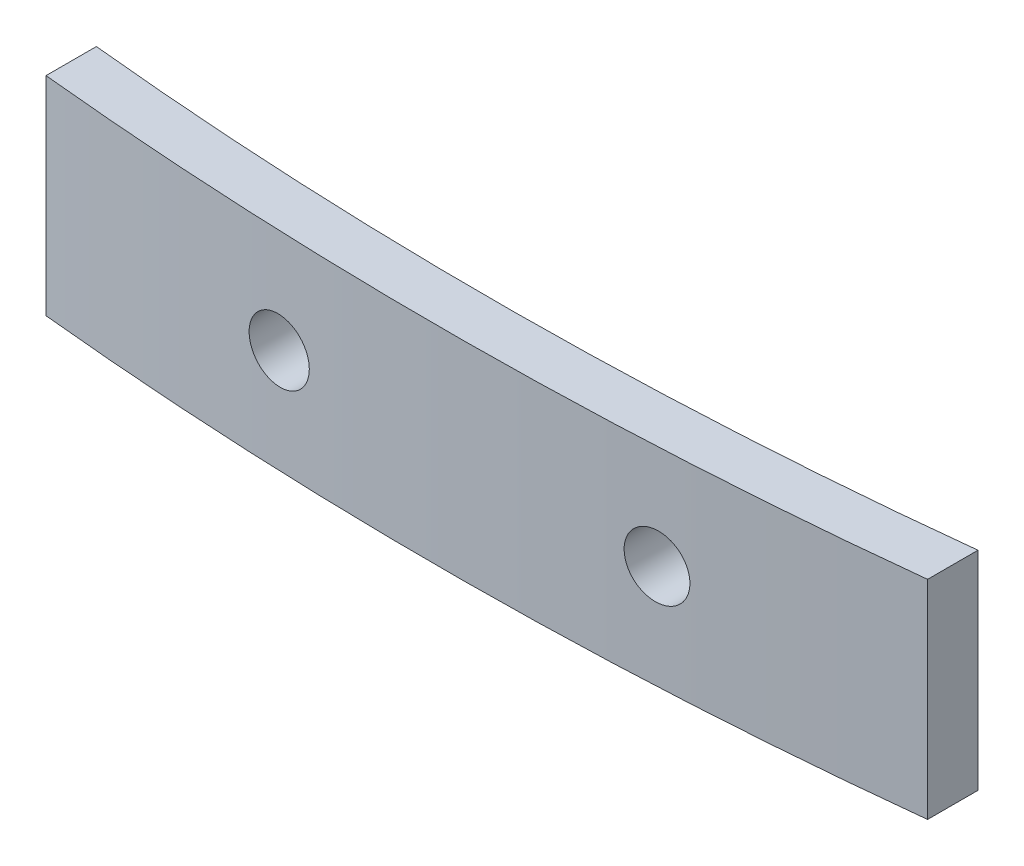
SolidWorks part; units mm, degrees
ref_plane "Front Plane" through (0, 0, 0) normal (0, 0, 1) x (1, 0, 0)
ref_plane "Top Plane" through (0, 0, 0) normal (0, 1, 0) x (1, 0, 0)
ref_plane "Right Plane" through (0, 0, 0) normal (1, 0, 0) x (0, 0, -1)
sketch "Sketch1" plane through (0, 0, 0) normal (0, 1, 0) x (1, 0, 0)
  line L0 (-35, 4.1426) -> (35, 4.5206) construction
  line L3 (-17.5, 11.9983) -> (-17.5, -12.2949) construction
  line L9 (-22.5, 11.9983) -> (-22.5, -12.2817) construction
  line L10 (22.5, 11.9983) -> (22.5, -13.4183) construction
  line L11 (17.5, 11.9983) -> (17.5, -13.4183) construction
  line L13 (-17.5, 0.1395) -> (-17.5, -1.8705)
  line L14 (17.5, 0.3238) -> (17.5, -1.6885)
  arc A4 (-17.5, 0.1395) -> (17.5, 0.3238) centre (-0.865, 164.5106) ccw
  arc A5 (-17.5, -1.8705) -> (17.5, -1.6885) centre (-0.865, 164.5106) ccw
  arc A7 (-35, 2.8648) -> (35, 3.2398) centre (-0.865, 164.5106) ccw construction
  arc A9 (-35.4132, 0.908) -> (35.4342, 1.2875) centre (-0.865, 164.5106) ccw construction
  point P4 (-35, 4.1426)
  point P7 (38.108, 5.4708)
  point P8 (35, 4.5206)
  point P18 (-31.892, 5.0928)
  dimension "D1" = 45
  dimension "D2" = 22.5
  dimension "D3" = 70
  dimension "D4" = 35
  dimension "D6" = 17.5
  dimension "D5" = 35
  dimension "D7" = 2
extrude "Boss-Extrude1" add sketch "Sketch1" along normal blind 8.3
sketch "Sketch2" plane through (0, 0, 0) normal (0, 0, 1) x (1, 0, 0)
  line L0 (0, 8.3) -> (0, 0) construction
  line L1 (17.5, 8.3) -> (-17.5, 8.3) construction
  circle A0 centre (7.5, 4.15) radius 1.25
  circle A1 centre (-7.5, 4.15) radius 1.25
  point P15 (0, 4.15)
  dimension "D2" = 2.5
  dimension "D3" = 2.5
  dimension "D1" = 15
  dimension "D4" = 7.5
extrude "Cut-Extrude1" cut sketch "Sketch2" against normal through all both and the other way through all
